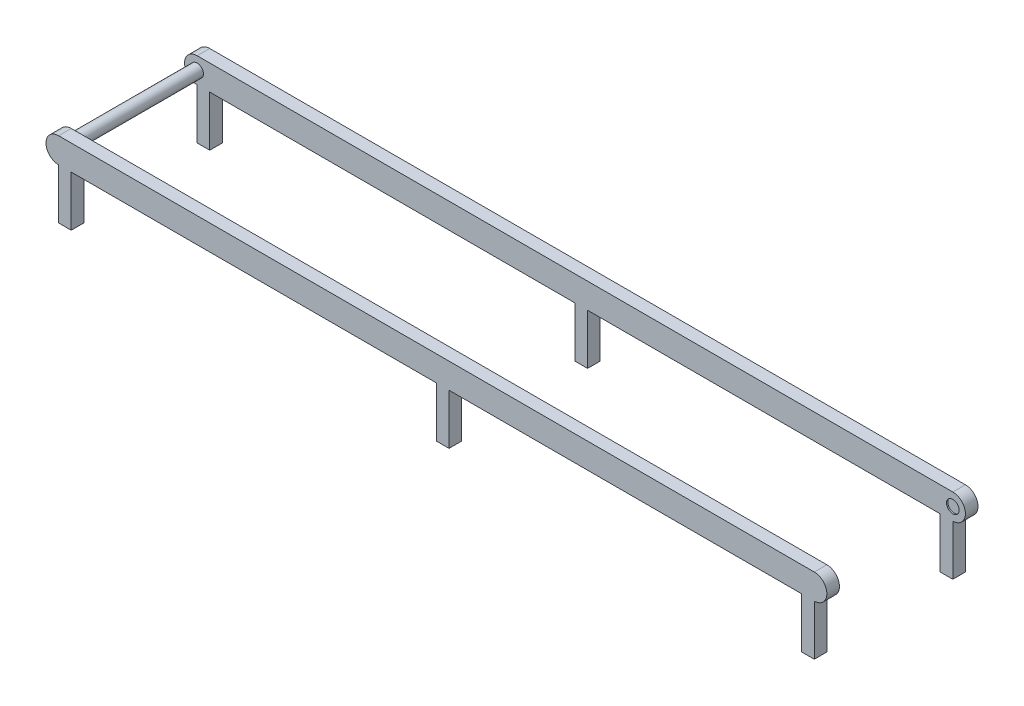
SolidWorks part; units mm, degrees
ref_plane "Alzado" through (0, 0, 0) normal (0, 0, 1) x (1, 0, 0)
ref_plane "Planta" through (0, 0, 0) normal (0, 1, 0) x (1, 0, 0)
ref_plane "Vista lateral" through (0, 0, 0) normal (1, 0, 0) x (0, 0, -1)
sketch "Croquis1" plane through (0, 0, 0) normal (0, 0, 1) x (1, 0, 0)
  line L0 (-300, 0) -> (300, 0) construction
  line L1 (-300, 10) -> (300, 10)
  line L2 (-300, -10) -> (300, -10)
  arc A0 (-300, 10) -> (-300, -10) centre (-300, 0) ccw
  arc A1 (300, -10) -> (300, 10) centre (300, 0) ccw
  point P2 (0, 0)
  dimension "D2" = 10
  dimension "D1" = 600
extrude "Saliente-Extruir1" add sketch "Croquis1" along normal blind 10
sketch "Croquis2" plane through (0, 0, 10) normal (0, 0, 1) x (1, 0, 0)
  circle A0 centre (-300, 0) radius 5
  dimension "D1" = 10
extrude "Saliente-Extruir2" add sketch "Croquis2" along normal blind 100
sketch "Croquis5" plane through (0, 0, 10) normal (0, 0, 1) x (1, 0, 0)
  circle A0 centre (300, 0) radius 5
  arc A1 (300, -10) -> (300, 10) centre (300, 0) ccw construction
  dimension "D1" = 10
  dimension "D2" = 0
extrude "Cortar-Extruir1" cut sketch "Croquis5" against normal blind 1
sketch "Croquis6" plane through (0, 0, 110) normal (0, 0, 1) x (1, 0, 0)
  line L0 (-300, -10) -> (300, -10) construction
  line L1 (300, 10) -> (-300, 10) construction
  line L2 (-300, -10) -> (300, -10)
  line L3 (300, 10) -> (-300, 10)
  arc A0 (300, -10) -> (300, 10) centre (300, 0) ccw construction
  arc A1 (-300, 10) -> (-300, -10) centre (-300, 0) ccw construction
  arc A2 (300, -10) -> (300, 10) centre (300, 0) ccw
  arc A3 (-300, 10) -> (-300, -10) centre (-300, 0) ccw
extrude "Saliente-Extruir5" add sketch "Croquis6" along normal blind 10
sketch "Croquis7" plane through (0, -10, 0) normal (0, -1, 0) x (1, 0, 0)
  line L0 (-300, 0) -> (300, 0) construction
  line L1 (-300, 10) -> (-290, 10)
  line L2 (-300, 10) -> (-300, 0)
  line L3 (-300, 0) -> (-290, 0)
  line L4 (-290, 10) -> (-290, 0)
  line L5 (-300, 10) -> (300, 10) construction
  line L6 (300, 0) -> (290, 0)
  line L7 (300, 0) -> (300, 10)
  line L8 (300, 10) -> (290, 10)
  line L9 (290, 0) -> (290, 10)
  line L10 (-300, 120) -> (300, 120) construction
  line L11 (300, 110) -> (290, 110)
  line L12 (300, 110) -> (300, 120)
  line L13 (300, 120) -> (290, 120)
  line L14 (290, 110) -> (290, 120)
  line L15 (-305, 110) -> (-295, 110) construction
  line L16 (-300, 110) -> (-290, 110)
  line L17 (-300, 110) -> (-300, 120)
  line L18 (-300, 120) -> (-290, 120)
  line L19 (-290, 110) -> (-290, 120)
  line L20 (-300, 110) -> (300, 110) construction
  line L21 (0, 0) -> (10, 0)
  line L22 (0, 0) -> (0, 10)
  line L23 (0, 10) -> (10, 10)
  line L24 (10, 0) -> (10, 10)
  line L25 (10, 110) -> (0, 110)
  line L26 (10, 110) -> (10, 120)
  line L27 (10, 120) -> (0, 120)
  line L28 (0, 110) -> (0, 120)
  dimension "D1" = 10
  dimension "D2" = 10
  dimension "D3" = 10
  dimension "D4" = 10
  dimension "D5" = 10
  dimension "D6" = 10
extrude "Saliente-Extruir6" add sketch "Croquis7" along normal blind 40 contours L17 L16 L19 L18 | L2 L1 L4 L3 | L7 L6 L9 L8 | L12 L11 L14 L13 | L26 L25 L28 L27 | L22 L21 L24 L23
